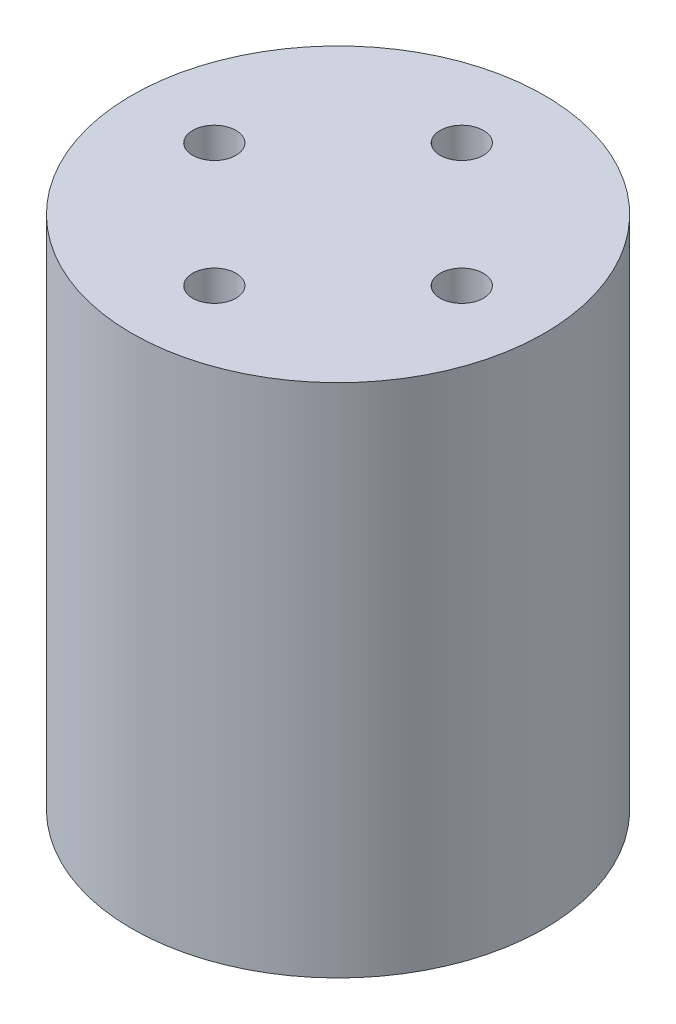
SolidWorks part; units mm, degrees
material "Plain Carbon Steel"
ref_plane "Front Plane" through (0, 0, 0) normal (0, 0, 1) x (1, 0, 0)
ref_plane "Top Plane" through (0, 0, 0) normal (0, 1, 0) x (1, 0, 0)
ref_plane "Right Plane" through (0, 0, 0) normal (1, 0, 0) x (0, 0, -1)
sketch "Sketch1" plane through (0, 0, 0) normal (0, 1, 0) x (1, 0, 0)
  circle A0 centre (0, 0) radius 20
  dimension "D1" = 40
extrude "Boss-Extrude1" add sketch "Sketch1" along normal mid plane 50
sketch "Sketch2" plane through (0, 25, 0) normal (0, 1, 0) x (1, 0, 0)
  line L0 (0, 20) -> (0, -20) construction
  line L1 (-20, 0) -> (20, 0) construction
  circle A0 centre (0, 0) radius 12
  circle A1 centre (0, 0) radius 20 construction
  dimension "D1" = 24
hole_wizard "M5x0.8 Tapped Hole1" positions "3DSketch1" profile "Sketch3" tap size "M5x0.8" standard "ANSI Metric"
sketch3d "3DSketch1"
  line L0 (0, 25, -20) -> (0, 25, 20) construction
  line L1 (-20, 25, 0) -> (20, 25, 0) construction
  circle A0 centre (0, 25, 0) radius 12 construction
  point P0 (0, 25, -12)
  point P4 (0, 37, 0)
  point P7 (12, 25, 0)
  point P11 (0, 25, 12)
  point P13 (-12, 25, 0)
sketch "Sketch3" plane through (0, 25, -12) normal (1, 0, 0) x (0, 0, 1)
  line L0 (0, 0) -> (0, 20)
  line L1 (0, 20) -> (2.1, 18.7382)
  line L2 (2.1, 18.7382) -> (2.1, 0)
  line L5 (2.1, 0) -> (0, 0)
  line L10 (0, 20) -> (-2.1, 18.7382) construction
  line L11 (0, -6.35) -> (0, 107.95) construction
  dimension "Tap Drill Dia." = 4.2
  dimension "Tap Drill Depth" = 20
  dimension "Drill Angle" = 118
cosmetic thread "Hole Thread1" parameters "D1"=10, "D2"=5
cosmetic thread "Hole Thread2" parameters "D1"=10, "D2"=5
cosmetic thread "Hole Thread3" parameters "D1"=10, "D2"=5
cosmetic thread "Hole Thread4" parameters "D1"=10, "D2"=5
ref_plane "Plane1" through (0, 25, 0) normal (0, 1, 0) x (1, 0, 0)
sketch "Sketch4" plane through (0, 25, 0) normal (0, 1, 0) x (1, 0, 0)
  circle A1 centre (0, 0) radius 20 construction
  circle A3 centre (0, 0) radius 20
